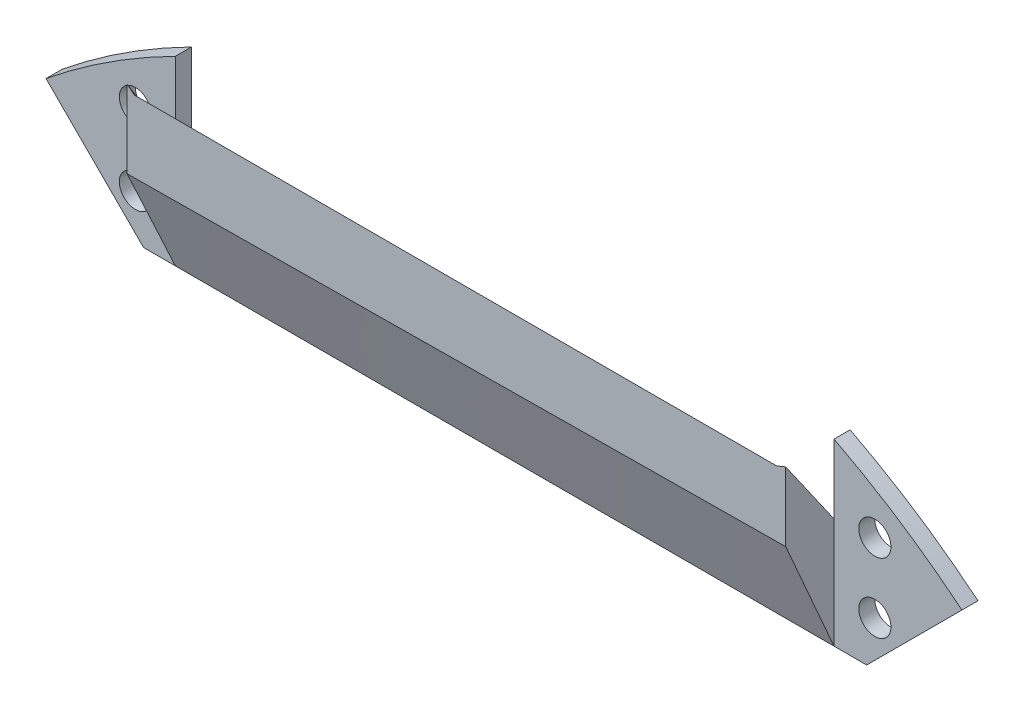
SolidWorks part; units mm, degrees
ref_plane "Front Plane" through (0, 0, 0) normal (0, 0, 1) x (1, 0, 0)
ref_plane "Top Plane" through (0, 0, 0) normal (0, 1, 0) x (1, 0, 0)
ref_plane "Right Plane" through (0, 0, 0) normal (1, 0, 0) x (0, 0, -1)
sketch "Model" plane through (0, 0, 0) normal (0, 0, 1) x (1, 0, 0)
  line L0 (265.571, 46.228) -> (275.731, 56.388)
  line L1 (387.491, 140.716) -> (398.667, 148.844)
  line L2 (349.899, 55.88) -> (359.551, 46.228)
  line L3 (379.871, 94.488) -> (394.603, 85.344)
  line L4 (349.899, 55.88) -> (379.871, 94.488)
  line L5 (358.027, 180.34) -> (369.711, 192.024)
  line L6 (239.155, 141.732) -> (268.111, 180.34)
  line L7 (245.759, 94.488) -> (275.731, 56.388)
  line L8 (227.471, 150.368) -> (239.155, 141.732)
  line L9 (231.027, 84.836) -> (245.759, 94.488)
  line L10 (272.0625, 193.262) -> (272.0625, 202.914)
  line L11 (255.919, 192.532) -> (268.111, 180.34)
  line L12 (353.963, 194.056) -> (353.963, 202.184)
  line L13 (277.763, 185.928) -> (347.867, 185.928)
  line L14 (272.0625, 193.262) -> (277.763, 185.928)
  line L15 (347.867, 185.928) -> (353.963, 194.056)
  line L16 (358.027, 180.34) -> (387.491, 140.716)
  circle A0 centre (288.285, 50.903) radius 0.35
  circle A1 centre (288.285, 47.903) radius 0.35
  circle A2 centre (313.04, 43.867) radius 0.35
  circle A3 centre (313.04, 40.867) radius 0.35
  circle A4 centre (338.328, 47.752) radius 0.35
  circle A5 centre (338.328, 50.752) radius 0.35
  circle A6 centre (388.747, 117.475) radius 0.35
  circle A7 centre (385.747, 117.475) radius 0.35
  circle A8 centre (235.939, 117.475) radius 0.35
  circle A9 centre (238.939, 117.475) radius 0.35
  circle A10 centre (282.458, 118.999) radius 0.35
  circle A11 centre (282.458, 115.999) radius 0.35
  circle A12 centre (289.914, 95.9) radius 0.35
  circle A13 centre (292.914, 95.9) radius 0.35
  circle A14 centre (312.938, 85.446) radius 0.35
  circle A15 centre (312.938, 88.446) radius 0.35
  circle A16 centre (332.915, 95.885) radius 0.35
  circle A17 centre (335.915, 95.885) radius 0.35
  circle A18 centre (343.423, 119.026) radius 0.35
  circle A19 centre (343.423, 116.026) radius 0.35
  circle A20 centre (335.94, 139.075) radius 0.35
  circle A21 centre (332.94, 139.075) radius 0.35
  circle A22 centre (292.916, 138.918) radius 0.35
  circle A23 centre (289.916, 138.918) radius 0.35
  circle A24 centre (337.942, 181.002) radius 0.35
  circle A25 centre (337.942, 178.002) radius 0.35
  circle A26 centre (313.05, 149.379) radius 0.35
  circle A27 centre (313.05, 146.379) radius 0.35
  circle A28 centre (313.558, 171.817) radius 0.35
  circle A29 centre (313.558, 168.817) radius 0.35
  circle A30 centre (286.004, 181.078) radius 0.35
  circle A31 centre (286.004, 178.078) radius 0.35
  circle A32 centre (326.3085, 83.1484) radius 0.55
  circle A33 centre (328.2542, 81.5157) radius 0.55
  circle A34 centre (330.2, 79.883) radius 0.55
  circle A35 centre (332.1457, 78.2503) radius 0.55
  circle A36 centre (334.0915, 76.6176) radius 0.55
  circle A37 centre (336.0373, 74.985) radius 0.55
  circle A38 centre (337.983, 73.3523) radius 0.55
  circle A39 centre (339.9288, 71.7196) radius 0.55
  circle A40 centre (265.571, 46.228) radius 0.125
  circle A41 centre (275.731, 56.388) radius 0.125
  circle A42 centre (387.491, 140.716) radius 0.125
  circle A43 centre (398.667, 148.844) radius 0.125
  circle A44 centre (349.899, 55.88) radius 0.125
  circle A45 centre (359.551, 46.228) radius 0.125
  circle A46 centre (379.871, 94.488) radius 0.125
  circle A47 centre (394.603, 85.344) radius 0.125
  circle A48 centre (349.899, 55.88) radius 0.125
  circle A49 centre (379.871, 94.488) radius 0.125
  circle A50 centre (358.027, 180.34) radius 0.125
  circle A51 centre (369.711, 192.024) radius 0.125
  circle A52 centre (239.155, 141.732) radius 0.125
  circle A53 centre (268.111, 180.34) radius 0.125
  circle A54 centre (245.759, 94.488) radius 0.125
  circle A55 centre (275.731, 56.388) radius 0.125
  circle A56 centre (227.471, 150.368) radius 0.125
  circle A57 centre (239.155, 141.732) radius 0.125
  circle A58 centre (231.027, 84.836) radius 0.125
  circle A59 centre (245.759, 94.488) radius 0.125
  circle A60 centre (272.0625, 193.262) radius 0.2
  circle A61 centre (272.0625, 202.914) radius 0.2
  circle A62 centre (255.919, 192.532) radius 0.125
  circle A63 centre (268.111, 180.34) radius 0.125
  circle A64 centre (353.963, 194.056) radius 0.2
  circle A65 centre (353.963, 202.184) radius 0.2
  circle A66 centre (277.763, 185.928) radius 0.2
  circle A67 centre (347.867, 185.928) radius 0.2
  circle A68 centre (272.0625, 193.262) radius 0.2
  circle A69 centre (277.763, 185.928) radius 0.2
  circle A70 centre (347.867, 185.928) radius 0.2
  circle A71 centre (353.963, 194.056) radius 0.2
  circle A72 centre (358.027, 180.34) radius 0.125
  circle A73 centre (387.491, 140.716) radius 0.125
  circle A74 centre (312.547, 118.364) radius 10
  circle A75 centre (322.547, 118.364) radius 0.125
  circle A76 centre (302.547, 118.364) radius 0.125
  arc A77 (272.0625, 202.914) -> (353.9423, 202.6508) centre (312.7448, 122.6335) ccw
  circle A78 centre (353.9423, 202.6508) radius 0.2
  circle A79 centre (272.0621, 202.9138) radius 0.2
  circle A80 centre (341.009, 84.201) radius 2.5
  circle A81 centre (227.2882, 125.7761) radius 2
  circle A82 centre (227.1612, 118.1561) radius 2
  circle A83 centre (227.711, 110.744) radius 2
  circle A84 centre (227.8719, 133.9959) radius 2
  circle A85 centre (278.0556, 43.4621) radius 2
  circle A86 centre (295.1546, 37.9063) radius 2
  circle A87 centre (330.9154, 37.9063) radius 2
  circle A88 centre (348.0144, 43.4621) radius 2
  circle A89 centre (398.1981, 110.0581) radius 2
  circle A90 centre (399.035, 122.027) radius 2
  circle A91 centre (398.1981, 133.9959) radius 2
  circle A92 centre (395.859, 97.917) radius 2
  circle A93 centre (228.854, 102.997) radius 2
  circle A94 centre (231.013, 94.996) radius 2
  circle A95 centre (271.145, 46.736) radius 2
  circle A96 centre (286.258, 40.386) radius 2
  circle A97 centre (303.911, 36.322) radius 2
  circle A98 centre (322.072, 36.322) radius 2
  circle A99 centre (339.344, 40.386) radius 2
  circle A100 centre (354.076, 47.244) radius 2
  circle A101 centre (393.319, 90.043) radius 2
  circle A102 centre (396.367, 143.256) radius 2
  circle A103 centre (229.235, 144.018) radius 2
  circle A104 centre (313.035, 36.027) radius 2
  circle A105 centre (284.099, 152.527) radius 2.5
  circle A106 centre (272.288, 134.493) radius 2.5
  circle A107 centre (343.027, 152.273) radius 2.5
  circle A108 centre (258.6243, 93.2791) radius 2
  circle A109 centre (324.88, 146.685) radius 2
  circle A110 centre (299.988, 146.685) radius 2
  circle A111 centre (323.864, 177.165) radius 2
  circle A112 centre (301.512, 177.165) radius 2
  circle A113 centre (272.81, 98.425) radius 2.5
  circle A114 centre (352.806, 135.763) radius 2.5
  circle A115 centre (285.6744, 84.5154) radius 2.5
  circle A116 centre (252.871, 143.764) radius 2
  circle A117 centre (355.487, 167.64) radius 2
  circle A118 centre (277.4203, 69.9111) radius 2
  circle A119 centre (348.375, 69.596) radius 2
  circle A120 centre (373.775, 142.748) radius 2
  circle A121 centre (367.171, 93.472) radius 2
  circle A122 centre (270.651, 168.148) radius 2
  circle A123 centre (267.095, 185.928) radius 2
  circle A124 centre (359.043, 185.928) radius 2
  circle A125 centre (352.185, 97.917) radius 2.5
  circle A126 centre (324.88, 152.781) radius 2.5
  circle A127 centre (299.988, 152.781) radius 2.5
  circle A128 centre (323.864, 182.245) radius 2
  circle A129 centre (312.815, 96.52) radius 2
  circle A130 centre (312.815, 101.6) radius 2
  circle A131 centre (359.043, 194.564) radius 2
  circle A132 centre (301.512, 182.245) radius 2
  circle A133 centre (267.095, 195.072) radius 2
  circle A134 centre (312.547, 154.813) radius 1.75
sketch "Sketch2" plane through (0, 0, 0) normal (0, 0, 1) x (1, 0, 0)
  line L0 (369.8693, 192.1806) -> (358.027, 180.34)
  line L1 (255.978, 192.4729) -> (268.111, 180.34)
  line L3 (353.963, 202.6401) -> (353.963, 194.056)
  line L4 (353.963, 194.056) -> (347.867, 185.928)
  line L5 (347.867, 185.928) -> (277.763, 185.928)
  line L6 (277.763, 185.928) -> (272.0625, 193.262)
  line L7 (272.0625, 193.262) -> (272.0625, 202.914)
  line L10 (268.111, 180.34) -> (358.027, 180.34)
  arc A0 (272.0625, 202.914) -> (255.978, 192.4729) centre (312.7448, 122.6335) ccw
  arc A1 (272.0625, 202.914) -> (353.9423, 202.6508) centre (312.7448, 122.6335) ccw construction
  arc A3 (369.8693, 192.1806) -> (353.963, 202.6401) centre (312.7448, 122.6335) ccw
extrude "Boss-Extrude1" add sketch "Sketch2" along normal blind 2
sketch "Sketch4" plane through (0, 0, 0) normal (0, 0, -1) x (-1, 0, 0)
  circle A0 centre (-359.043, 194.564) radius 2
  circle A1 centre (-359.043, 185.928) radius 2
  circle A6 centre (-267.095, 185.928) radius 2
  circle A7 centre (-267.095, 195.072) radius 2
extrude "Cut-Extrude2" cut sketch "Sketch4" against normal through all
ref_plane "Plane1" through (0, 0, 8) normal (0, 0, 1) x (1, 0, 0)
sketch "Sketch5" plane through (0, 0, 2) normal (0, 0, 1) x (1, 0, 0)
  line L0 (272.0625, 193.262) -> (272.0625, 180.34)
  line L1 (268.111, 180.34) -> (358.027, 180.34) construction
  line L2 (272.0625, 180.34) -> (353.963, 180.34)
  line L3 (353.963, 180.34) -> (353.963, 194.056)
  line L4 (353.963, 194.056) -> (347.867, 185.928)
  line L5 (347.867, 185.928) -> (277.763, 185.928)
  line L6 (277.763, 185.928) -> (272.0625, 193.262)
sketch "Sketch6" plane through (0, 0, 8) normal (0, 0, 1) x (1, 0, 0)
  line L0 (272.0625, 202.914) -> (272.0625, 193.262)
  line L1 (272.0625, 193.262) -> (353.963, 194.056)
  line L2 (353.963, 194.056) -> (353.963, 202.6401)
  line L4 (272.0625, 202.914) -> (272.9684, 202.1846)
  line L5 (272.9684, 202.1846) -> (352.8084, 202.1846)
  line L6 (352.8084, 202.1846) -> (353.963, 202.6401)
loft "Loft4" add profiles "Sketch5", "Sketch6"
